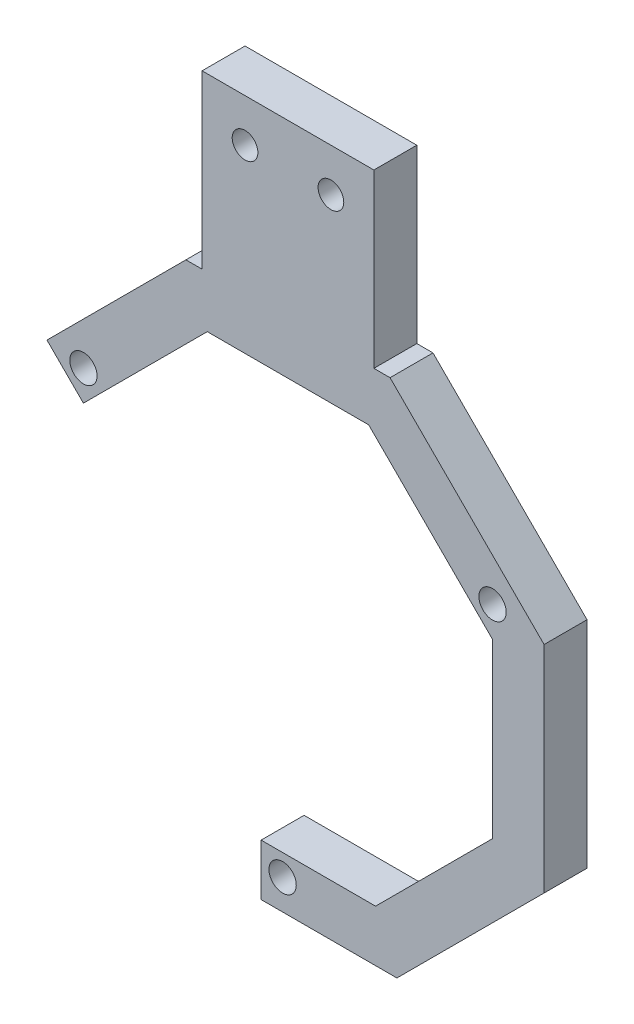
SolidWorks part; units mm, degrees
ref_plane "Front Plane" through (0, 0, 0) normal (0, 0, 1) x (1, 0, 0)
ref_plane "Top Plane" through (0, 0, 0) normal (0, 1, 0) x (1, 0, 0)
ref_plane "Right Plane" through (0, 0, 0) normal (1, 0, 0) x (0, 0, -1)
sketch "Sketch1" plane through (0, 0, 0) normal (0, 0, 1) x (1, 0, 0)
  line L0 (0, 0) -> (-65.0886, 37.5789) construction
  line L1 (0, 0) -> (0, -60.0043) construction
  line L2 (0, 0) -> (74.0703, 42.7645) construction
  line L3 (-35.6341, 17.238) -> (-15.0896, 37.7825)
  line L4 (-15.0896, 37.7825) -> (-12.7, 37.7825)
  line L5 (15.0896, 37.7825) -> (37.8659, 15.0061)
  line L6 (-35.6341, 17.238) -> (-30.2459, 11.8498)
  line L7 (-30.2459, 11.8498) -> (-11.9333, 30.1625)
  line L8 (-11.9333, 30.1625) -> (11.9333, 30.1625)
  line L9 (11.9333, 30.1625) -> (30.2459, 11.8498)
  line L10 (30.2459, 11.8498) -> (30.2459, -13.6593)
  line L11 (30.2459, -13.6593) -> (12.949, -30.9562)
  line L12 (37.8659, 15.0061) -> (37.8659, -16.8156)
  line L13 (37.8659, -16.8156) -> (16.1053, -38.5763)
  line L14 (12.949, -30.9562) -> (-3.9687, -30.9563)
  line L15 (-3.9687, -30.9563) -> (-3.9687, -38.5763)
  line L16 (-3.9687, -38.5763) -> (16.1053, -38.5763)
  line L17 (-12.7, 37.7825) -> (-12.7, 63.1825)
  line L18 (12.7, 37.7825) -> (12.7, 63.1825)
  line L19 (0, 30.1625) -> (0, 60.2692) construction
  line L20 (-12.7, 63.1825) -> (12.7, 63.1825)
  line L21 (12.7, 37.7825) -> (15.0896, 37.7825)
  circle A0 centre (-30.2459, 17.4625) radius 6.35 construction
  circle A1 centre (0, 0) radius 28.575 construction
  circle A2 centre (30.2459, 17.4625) radius 6.35 construction
  circle A3 centre (0, -34.925) radius 6.35 construction
  dimension "D1" = 12.7
  dimension "D2" = 57.15
  dimension "D5" = 12.7
  dimension "D6" = 12.7
  dimension "D3" = 120
  dimension "D4" = 120
  dimension "D7" = 135
  dimension "D8" = 135
  dimension "D9" = 7.62
  dimension "D10" = 7.62
  dimension "D11" = 3.9688
  dimension "D12" = 7.62
  dimension "D13" = 3.9688
  dimension "D14" = 20.32
  dimension "D15" = 3.9688
  dimension "D16" = 7.62
  dimension "D17" = 7.62
  dimension "D18" = 135
  dimension "D19" = 6.35
  dimension "D20" = 7.62
  dimension "D21" = 7.62
  dimension "D22" = 3.9688
  dimension "D23" = 3.9688
  dimension "D24" = 25.4
  dimension "D25" = 12.7
  dimension "D26" = 25.4
extrude "Boss-Extrude1" add sketch "Sketch1" along normal blind 6.35
hole_wizard "#10-32 Tapped Hole1" positions "Sketch3" profile "Sketch2" tap size "#10-32" standard "ANSI Inch" end condition through all
sketch "Sketch3" plane through (0, 0, 6.35) normal (0, 0, 1) x (1, 0, 0)
  line L0 (-30.2459, 11.8498) -> (-11.9333, 30.1625) construction
  line L1 (-35.6341, 17.238) -> (-30.2459, 11.8498) construction
  point P0 (-30.2459, 16.34)
  dimension "D1" = 3.175
  dimension "D2" = 3.175
sketch "Sketch2" plane through (-30.2459, 16.34, 6.35) normal (1, 0, 0) x (0, -1, 0)
  line L0 (0, 0) -> (0, 6.35)
  line L1 (0, 6.35) -> (2.0193, 6.35)
  line L2 (2.0193, 6.35) -> (2.0193, 0)
  line L5 (2.0193, 0) -> (0, 0)
  line L11 (0, -6.35) -> (0, 107.95) construction
  dimension "Thread Major Dia." = 4.0386
  dimension "Thru Tap Drill Depth" = 6.35
hole_wizard "#10-32 Tapped Hole2" positions "Sketch5" profile "Sketch4" tap size "#10-32" standard "ANSI Inch" end condition through all
sketch "Sketch5" plane through (0, 0, 6.35) normal (0, 0, 1) x (1, 0, 0)
  line L0 (-3.9687, -30.9563) -> (-3.9687, -38.5763) construction
  line L1 (12.949, -30.9562) -> (-3.9687, -30.9563) construction
  line L2 (11.9333, 30.1625) -> (30.2459, 11.8498) construction
  line L3 (-30.2459, 16.34) -> (-5.5991, 16.34) construction
  point P0 (30.2459, 16.34)
  point P2 (-0.7937, -34.1312)
  dimension "D1" = 3.175
  dimension "D2" = 3.175
  dimension "D3" = 3.175
sketch "Sketch4" plane through (30.2459, 16.34, 6.35) normal (1, 0, 0) x (0, -1, 0)
  line L0 (0, 0) -> (0, 6.35)
  line L1 (0, 6.35) -> (2.0193, 6.35)
  line L2 (2.0193, 6.35) -> (2.0193, 0)
  line L5 (2.0193, 0) -> (0, 0)
  line L11 (0, -6.35) -> (0, 107.95) construction
  dimension "Thread Major Dia." = 4.0386
  dimension "Thru Tap Drill Depth" = 6.35
hole_wizard "#6 Clearance Hole1" positions "3DSketch1" profile "Sketch6" hole size "#6" standard "ANSI Inch" end condition through all
sketch3d "3DSketch1"
  line L0 (12.7, 63.1825, 6.35) -> (-12.7, 63.1825, 6.35) construction
  line L1 (-12.7, 63.1825, 6.35) -> (-12.7, 37.7825, 6.35) construction
  line L2 (12.7, 37.7825, 6.35) -> (12.7, 63.1825, 6.35) construction
  point P0 (-6.35, 56.8325, 6.35)
  point P2 (6.35, 56.8325, 6.35)
  dimension "D1" = 6.35
  dimension "D2" = 6.35
  dimension "D3" = 6.35
  dimension "D4" = 6.35
sketch "Sketch6" plane through (-6.35, 56.8325, 6.35) normal (1, 0, 0) x (0, -1, 0)
  line L0 (0, 0) -> (0, 6.35)
  line L1 (0, 6.35) -> (1.8986, 6.35)
  line L2 (1.8986, 6.35) -> (1.8986, 0)
  line L5 (1.8986, 0) -> (0, 0)
  line L11 (0, -6.35) -> (0, 107.95) construction
  dimension "Thru Hole Dia." = 3.7973
  dimension "Thru Hole Depth" = 6.35
sketch "Sketch8" [suppressed] plane through (0, 0, 6.35) normal (0, 0, 1) x (1, 0, 0)
  circle A0 centre (0, 0) radius 34.6287 construction
